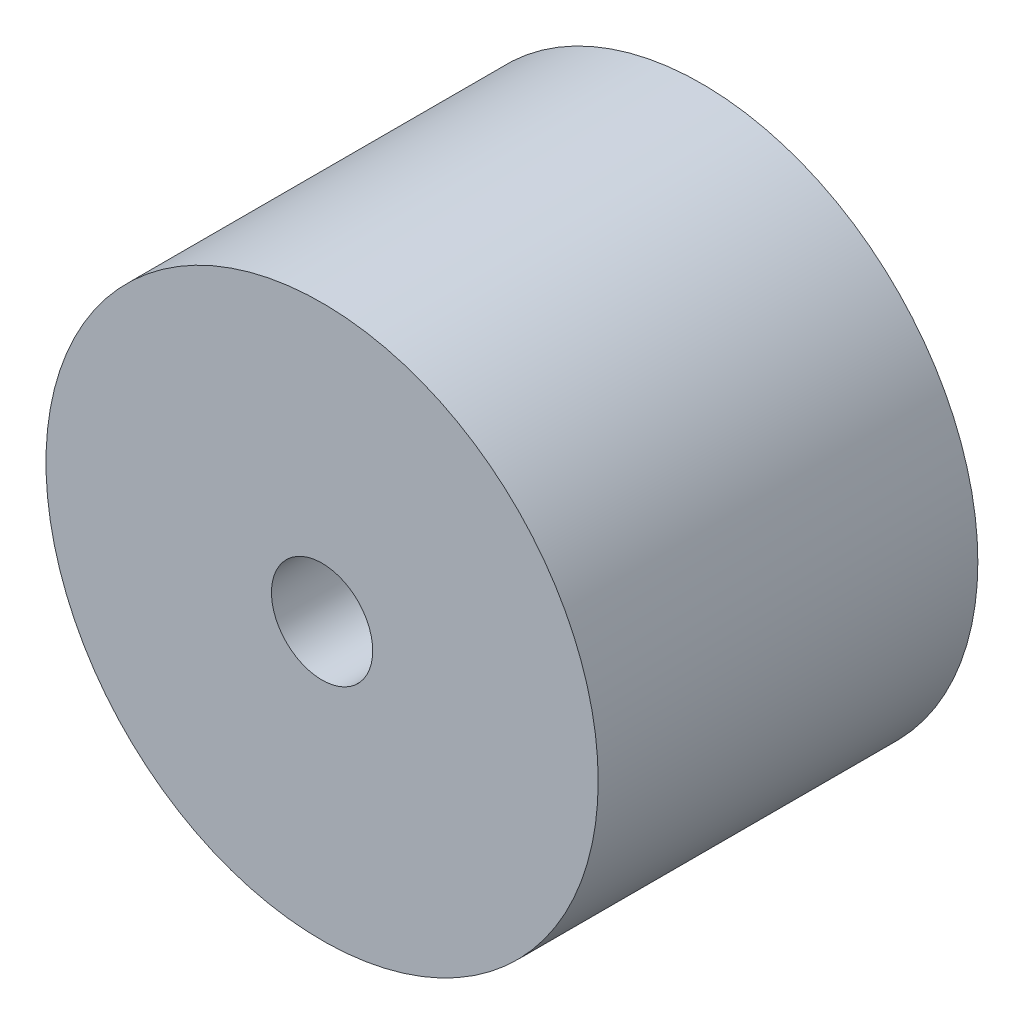
SolidWorks part; units mm, degrees
ref_plane "前视基准面" through (0, 0, 0) normal (0, 0, 1) x (1, 0, 0)
ref_plane "上视基准面" through (0, 0, 0) normal (0, 1, 0) x (1, 0, 0)
ref_plane "右视基准面" through (0, 0, 0) normal (1, 0, 0) x (0, 0, -1)
other "Configuration Table"
sketch "草图1" plane through (0, 0, 0) normal (0, 0, 1) x (1, 0, 0)
  circle A0 centre (0, 0) radius 4
  circle A1 centre (0, 0) radius 21.8182
  dimension "D1" = 8
extrude "凸台-拉伸1" add sketch "草图1" along normal blind 30
